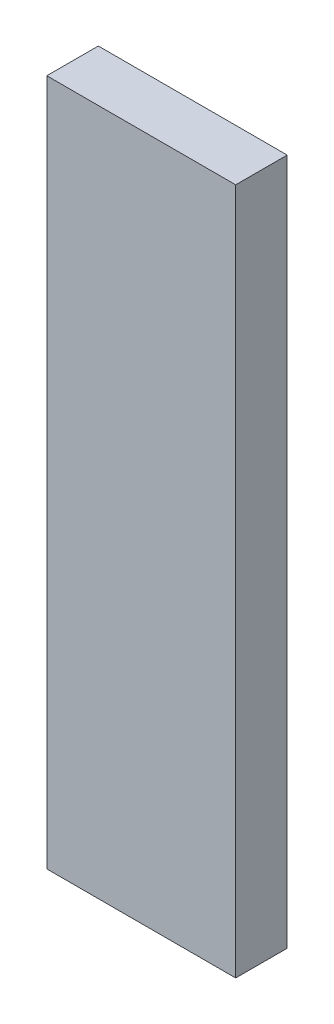
SolidWorks part; units mm, degrees
ref_plane "Front Plane" through (0, 0, 0) normal (0, 0, 1) x (1, 0, 0)
ref_plane "Top Plane" through (0, 0, 0) normal (0, 1, 0) x (1, 0, 0)
ref_plane "Right Plane" through (0, 0, 0) normal (1, 0, 0) x (0, 0, -1)
sketch "Sketch1" plane through (0, 0, 0) normal (0, 0, 1) x (1, 0, 0)
  line L1 (0, 0) -> (11, 0)
  line L2 (0, 0) -> (0, 40)
  line L3 (0, 40) -> (11, 40)
  line L4 (11, 0) -> (11, 40)
  dimension "D1" = 11
  dimension "D2" = 40
extrude "Boss-Extrude1" add sketch "Sketch1" along normal blind 3
